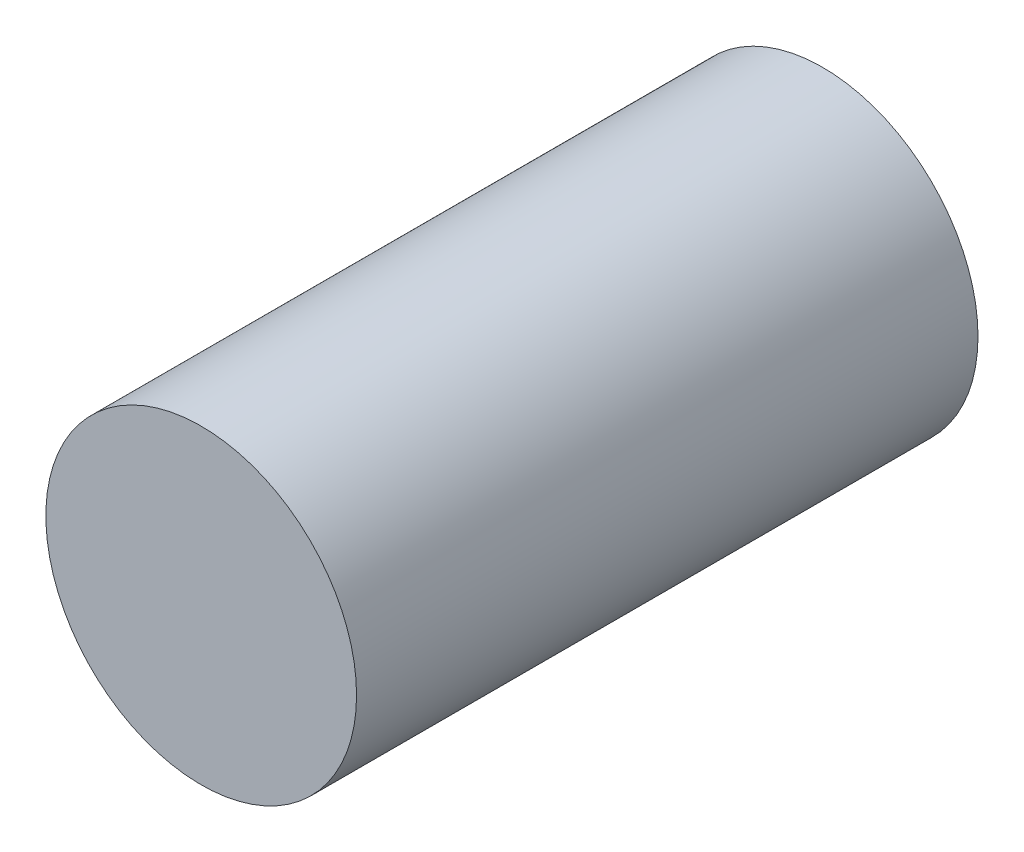
SolidWorks part; units mm, degrees
material "Titanium"
ref_plane "Front Plane" through (0, 0, 0) normal (0, 0, 1) x (1, 0, 0)
ref_plane "Top Plane" through (0, 0, 0) normal (0, 1, 0) x (1, 0, 0)
ref_plane "Right Plane" through (0, 0, 0) normal (1, 0, 0) x (0, 0, -1)
sketch "Sketch1" plane through (0, 0, 0) normal (0, 0, 1) x (1, 0, 0)
  circle A0 centre (0, 0) radius 10
  dimension "D1" = 20
extrude "Extrude1" add sketch "Sketch1" along normal blind 40
